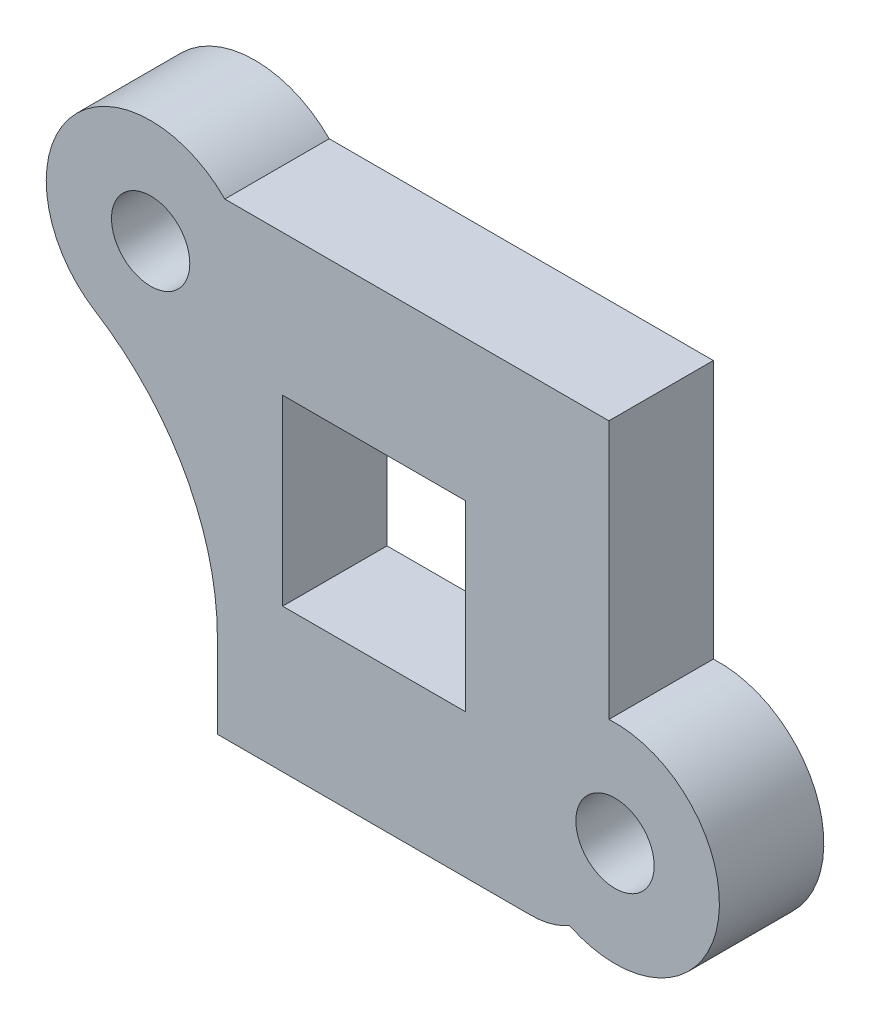
SolidWorks part; units mm, degrees
material "ABS"
ref_plane "Спереди" through (0, 0, 0) normal (0, 0, 1) x (1, 0, 0)
ref_plane "Сверху" through (0, 0, 0) normal (0, 1, 0) x (1, 0, 0)
ref_plane "Справа" through (0, 0, 0) normal (1, 0, 0) x (0, 0, -1)
sketch "Эскиз1" plane through (0, 0, 0) normal (0, 0, 1) x (1, 0, 0)
  line L0 (0.25, 9.4632) -> (11.25, 9.4632) construction
  line L1 (7.5, -9.4632) -> (-7.5, -9.4632)
  line L2 (7.5, -9.4632) -> (7.5, -8.43)
  line L3 (7.5, 9.4632) -> (-7.2147, 9.4632)
  line L4 (-7.5, -9.4632) -> (-7.5, 3.5724)
  line L5 (7.5, -9.4632) -> (-7.5, 9.4632) construction
  line L6 (7.5, 9.4632) -> (-7.5, -9.4632) construction
  line L7 (-7.5, 3.5724) -> (-7.5, 9.4632) construction
  line L8 (7.5, -0.4436) -> (7.5, 9.4632)
  line L9 (-7.5, 9.4632) -> (-7.2147, 9.4632) construction
  line L10 (7.5, -8.43) -> (7.5, -0.4436) construction
  line L11 (7.5, -0.4436) -> (7.5435, -0.3954) construction
  line L13 (-5, -2.9368) -> (2, -2.9368)
  line L14 (-5, -2.9368) -> (-5, 4.0632)
  line L15 (-5, 4.0632) -> (2, 4.0632)
  line L16 (2, -2.9368) -> (2, 4.0632)
  arc A0 (7.5, -8.43) -> (7.5, -0.4436) centre (7.7331, -4.4368) ccw
  arc A1 (-7.2147, 9.4632) -> (-7.5, 3.5724) centre (-10.0568, 6.6485) ccw
  arc A2 (-7.3174, 9.5632) -> (-12.7963, 9.5632) centre (-10.0568, 6.6485) ccw construction
  circle A3 centre (7.7331, -4.4368) radius 1.5
  circle A4 centre (-10.0568, 6.6485) radius 1.5
  circle A5 centre (7.7331, -4.4368) radius 1.5 construction
  point P0 (0, 0)
  dimension "D1" = 15
  dimension "D2" = 15
extrude "Бобышка-Вытянуть1" add sketch "Эскиз1" along normal blind 4
sketch "Эскиз2" plane through (0, 0, 0) normal (0, 0, -1) x (-1, 0, 0)
  line L0 (-4.5, -8.4368) -> (7.5, -8.4368) construction
  line L1 (7.5, -9.4632) -> (-7.5, -9.4632)
  line L2 (7.5, -9.4632) -> (7.5, -8.4368)
  line L3 (7.5, -8.4368) -> (-4.5, -8.4368)
  line L4 (-7.5, -9.4632) -> (-7.5, -8.43)
  arc A0 (-7.5, -8.43) -> (-5.9934, -8.0387) centre (-7.7331, -4.4368) ccw
  arc A1 (-5.9934, -8.0387) -> (-4.5, -8.4368) centre (-4.5, -5.4368) ccw
extrude "Вырез-Вытянуть1" cut sketch "Эскиз2" against normal through all
fillet "Скругление1" radius 10 1 edges at (-7.5, 3.5724, 2)
chamfer "Фаска1" distance 1.5 angle 45 2 edges at (-8.5568, 6.6485, 0) (9.2331, -4.4368, 0)
